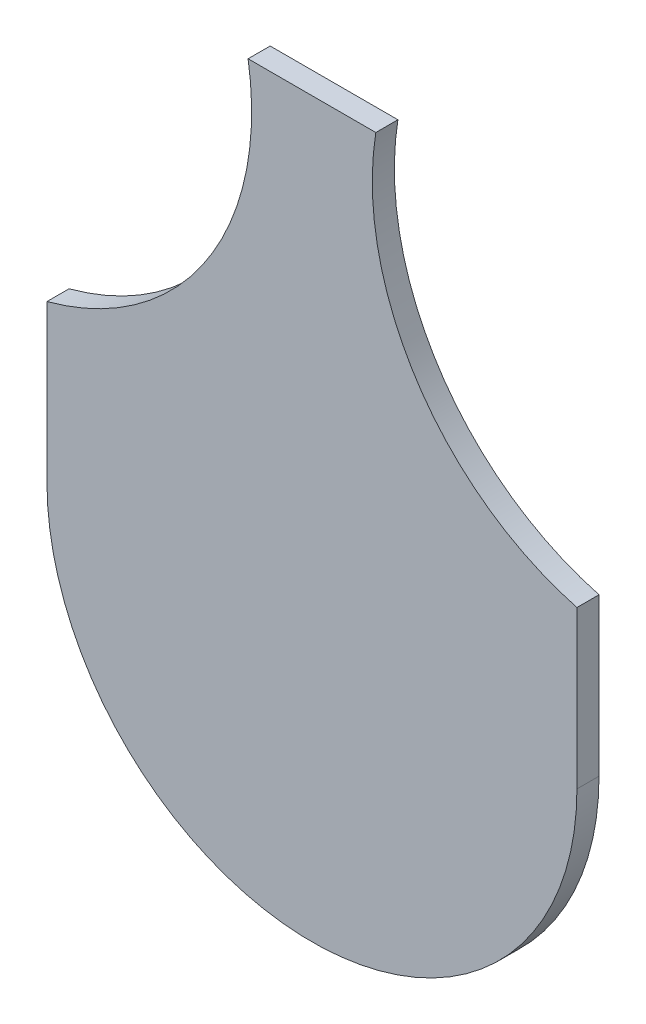
SolidWorks part; units mm, degrees
ref_plane "Front Plane" through (0, 0, 0) normal (0, 0, 1) x (1, 0, 0)
ref_plane "Top Plane" through (0, 0, 0) normal (0, 1, 0) x (1, 0, 0)
ref_plane "Right Plane" through (0, 0, 0) normal (1, 0, 0) x (0, 0, -1)
sketch "Sketch7" plane through (0, 0, 0) normal (0, 0, 1) x (1, 0, 0)
  line L11 (0, 105.9501) -> (0, 0) construction
  line L21 (-60, 0) -> (-60, 35.5745)
  line L22 (60, 0) -> (60, 35.5745)
  line L23 (-14.4618, 105.9501) -> (14.4618, 105.9501)
  arc A2 (-60, 35.5745) -> (-14.4618, 105.9501) centre (-76.1566, 95.9501) ccw
  arc A3 (60, 35.5745) -> (14.4618, 105.9501) centre (76.1566, 95.9501) cw
  arc A5 (-60, 0) -> (60, 0) centre (0, 0) ccw
  dimension "D1" = 62.5
  dimension "D2" = 28.9237
  dimension "D5" = 35.5745
  dimension "D7" = 120
  dimension "D3" = 35.5745
  dimension "D4" = 70.3756
  dimension "D6" = 70.3756
extrude "Boss-Extrude1" add sketch "Sketch7" along normal blind 5
